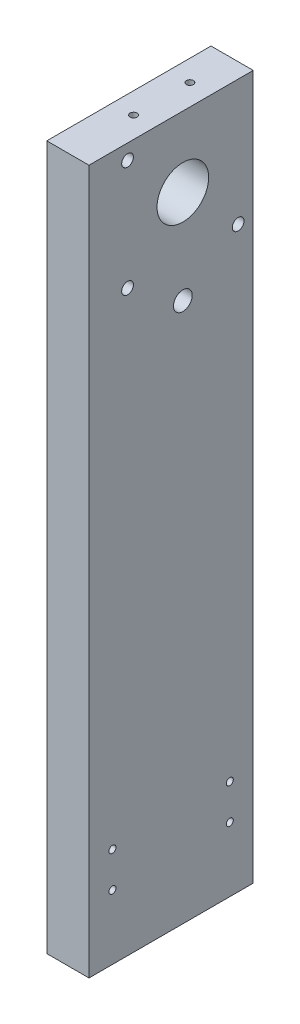
SolidWorks part; units mm, degrees
material "Bronce de aluminio"
ref_plane "Front Plane" through (0, 0, 0) normal (0, 0, 1) x (1, 0, 0)
ref_plane "Top Plane" through (0, 0, 0) normal (0, 1, 0) x (1, 0, 0)
ref_plane "Right Plane" through (0, 0, 0) normal (1, 0, 0) x (0, 0, -1)
sketch "Croquis1" plane through (0, 0, 0) normal (1, 0, 0) x (0, 0, -1)
  line L0 (35, 120) -> (5, 120) construction
  line L1 (35, -150) -> (-35, -150)
  line L2 (35, -150) -> (35, 150)
  line L3 (35, 150) -> (-35, 150)
  line L4 (-35, -150) -> (-35, 150)
  line L5 (35, -150) -> (-35, 150) construction
  line L6 (35, 150) -> (-35, -150) construction
  line L7 (5, 120) -> (5, 150) construction
  line L8 (5, 120) -> (28.57, 96.43) construction
  line L9 (5, 120) -> (-18.57, 143.57) construction
  line L10 (5, 120) -> (-18.57, 96.43) construction
  line L11 (-18.57, 143.57) -> (-18.57, 96.43) construction
  line L12 (-18.57, 96.43) -> (28.57, 96.43) construction
  line L13 (5, 120) -> (5, 80) construction
  line L14 (0, -150) -> (0, -115) construction
  line L16 (25, -122.5) -> (-25, -122.5) construction
  line L17 (25, -122.5) -> (25, -107.5) construction
  line L18 (25, -107.5) -> (-25, -107.5) construction
  line L19 (-25, -122.5) -> (-25, -107.5) construction
  line L20 (25, -122.5) -> (-25, -107.5) construction
  line L21 (25, -107.5) -> (-25, -122.5) construction
  circle A0 centre (5, 120) radius 11
  circle A1 centre (-18.57, 143.57) radius 2.5
  circle A2 centre (-18.57, 96.43) radius 2.5
  circle A3 centre (28.57, 96.43) radius 2.5
  circle A4 centre (5, 80) radius 4
  circle A5 centre (-25, -107.5) radius 1.5
  circle A6 centre (-25, -122.5) radius 1.5
  circle A7 centre (25, -122.5) radius 1.5
  circle A8 centre (25, -107.5) radius 1.5
  point P0 (0, 0)
  dimension "D4" = 22
  dimension "D6" = 5
  dimension "D8" = 8
  dimension "D12" = 3
  dimension "D1" = 300
  dimension "D2" = 70
  dimension "D3" = 30
  dimension "D5" = 47.14
  dimension "D7" = 40
  dimension "D9" = 50
  dimension "D10" = 15
  dimension "D11" = 35
sketch "Croquis2" plane through (0, 0, 0) normal (1, 0, 0) x (0, 0, -1)
  line L0 (35, 150) -> (-35, 150) construction
  line L1 (35, -150) -> (35, 150) construction
  line L2 (35, -150) -> (-35, -150) construction
  line L3 (-35, -150) -> (-35, 150) construction
  line L4 (35, 150) -> (-35, 150)
  line L5 (35, -150) -> (35, 150)
  line L6 (35, -150) -> (-35, -150)
  line L7 (-35, -150) -> (-35, 150)
  circle A0 centre (25, -122.5) radius 1.5 construction
  circle A1 centre (-25, -122.5) radius 1.5 construction
  circle A2 centre (25, -107.5) radius 1.5 construction
  circle A3 centre (-25, -107.5) radius 1.5 construction
  circle A4 centre (5, 80) radius 4 construction
  circle A5 centre (28.57, 96.43) radius 2.5 construction
  circle A6 centre (5, 120) radius 11 construction
  circle A7 centre (-18.57, 96.43) radius 2.5 construction
  circle A8 centre (-18.57, 143.57) radius 2.5 construction
  circle A9 centre (25, -122.5) radius 1.5
  circle A10 centre (-25, -122.5) radius 1.5
  circle A11 centre (25, -107.5) radius 1.5
  circle A12 centre (-25, -107.5) radius 1.5
  circle A13 centre (5, 80) radius 4
  circle A14 centre (28.57, 96.43) radius 2.5
  circle A15 centre (5, 120) radius 11
  circle A16 centre (-18.57, 96.43) radius 2.5
  circle A17 centre (-18.57, 143.57) radius 2.5
extrude "Saliente-Extruir1" add sketch "Croquis2" along normal blind 18
sketch "Croquis3" plane through (0, 150, 0) normal (0, 1, 0) x (1, 0, 0)
  line L0 (9, 35) -> (9, 5) construction
  line L2 (18, 35) -> (0, 35) construction
  line L4 (9, 5) -> (9, -7) construction
  circle A0 centre (9, -7) radius 1.5
  circle A1 centre (9, 17) radius 1.5
  dimension "D3" = 3
  dimension "D4" = 3
  dimension "D1" = 30
  dimension "D2" = 24
  dimension "D5" = 12
extrude "Cortar-Extruir1" cut sketch "Croquis3" against normal blind 14
extrude "Saliente-Extruir2" [suppressed] add sketch "Croquis1" along normal blind 9 contours A0 | L3 L4 L1 L2 | A7 | A8 | A5 | A6 | A4
sketch "Croquis4" [suppressed] plane through (0, 0, 0) normal (1, 0, 0) x (0, 0, -1)
  line L0 (35, -150) -> (-35, -150) construction
  line L1 (-35, -150) -> (-35, 150) construction
  line L2 (35, -150) -> (35, 150) construction
  line L3 (35, 150) -> (-35, 150) construction
  line L4 (35, -150) -> (-35, -150)
  line L5 (-35, -150) -> (-35, 150)
  line L6 (35, -150) -> (35, 150)
  line L7 (35, 150) -> (-35, 150)
  circle A0 centre (5, 80) radius 4 construction
  circle A1 centre (-25, -107.5) radius 1.5 construction
  circle A2 centre (-25, -122.5) radius 1.5 construction
  circle A3 centre (25, -122.5) radius 1.5 construction
  circle A4 centre (25, -107.5) radius 1.5 construction
  circle A5 centre (5, 80) radius 4
  circle A6 centre (-25, -107.5) radius 1.5
  circle A7 centre (-25, -122.5) radius 1.5
  circle A8 centre (25, -122.5) radius 1.5
  circle A9 centre (25, -107.5) radius 1.5
  circle A10 centre (5, 120) radius 4
  dimension "D1" = 8
extrude "Saliente-Extruir3" [suppressed] add sketch "Croquis4" against normal blind 9
sketch "Croquis5" [suppressed] plane through (0, 150, 0) normal (0, 1, 0) x (1, 0, 0)
  line L0 (0, 35) -> (0, 17) construction
  line L1 (9, 35) -> (-9, 35) construction
  line L2 (0, 17) -> (0, -7) construction
  circle A0 centre (0, 17) radius 1.5
  circle A1 centre (0, -7) radius 1.5
  dimension "D3" = 3
  dimension "D1" = 18
  dimension "D2" = 24
extrude "Cortar-Extruir2" [suppressed] cut sketch "Croquis5" against normal blind 14
sketch "Croquis6" [suppressed] plane through (0, 0, 0) normal (0, 0, 1) x (1, 0, 0)
  line L0 (0, 0) -> (-30, 0) construction
  line L1 (50, 125) -> (-50, 125)
  line L2 (50, 125) -> (50, -125)
  line L3 (50, -125) -> (-50, -125)
  line L4 (-50, 125) -> (-50, -125)
  line L5 (50, 125) -> (-50, -125) construction
  line L6 (50, -125) -> (-50, 125) construction
  line L7 (9, 12) -> (-9, 12) construction
  line L8 (9, 12) -> (9, -12) construction
  line L9 (9, -12) -> (-9, -12) construction
  line L10 (-9, 12) -> (-9, -12) construction
  line L11 (9, 12) -> (-9, -12) construction
  line L12 (9, -12) -> (-9, 12) construction
  line L13 (-30, 0) -> (-30, 40) construction
  line L14 (-39, 52) -> (-39, -28) construction
  line L15 (-21, 28) -> (-39, 28) construction
  line L16 (-21, 28) -> (-21, 52) construction
  line L17 (-21, 52) -> (-39, 52) construction
  line L18 (-39, 28) -> (-39, 52) construction
  line L19 (-21, 28) -> (-39, 52) construction
  line L20 (-21, 52) -> (-39, 28) construction
  circle A0 centre (-9, 12) radius 1.5
  circle A1 centre (9, 12) radius 1.5
  circle A2 centre (9, -12) radius 1.5
  circle A3 centre (-9, -12) radius 1.5
  circle A4 centre (-21, 28) radius 1.5
  circle A5 centre (-39, 28) radius 1.5
  circle A6 centre (-21, 52) radius 1.5
  circle A7 centre (-39, 52) radius 1.5
  circle A8 centre (21, 52) radius 1.5
  circle A9 centre (39, 52) radius 1.5
  circle A10 centre (21, 28) radius 1.5
  circle A11 centre (39, 28) radius 1.5
  circle A12 centre (-39, -28) radius 1.5
  circle A13 centre (-21, -28) radius 1.5
  circle A14 centre (-39, -52) radius 1.5
  circle A15 centre (-21, -52) radius 1.5
  circle A16 centre (21, -28) radius 1.5
  circle A17 centre (21, -52) radius 1.5
  circle A18 centre (39, -28) radius 1.5
  circle A19 centre (39, -52) radius 1.5
  point P0 (0, 0)
  point P6 (0, 0)
  dimension "D7" = 3
  dimension "D9" = 60
  dimension "D1" = 100
  dimension "D2" = 255
  dimension "D3" = 18
  dimension "D4" = 24
  dimension "D5" = 30
  dimension "D6" = 40
  dimension "D11" = 80
  dimension "D8" = 2
  dimension "D10" = 2
extrude "Saliente-Extruir4" [suppressed] add sketch "Croquis6" along normal blind 16
sketch "Croquis7" [suppressed] plane through (0, 0, 0) normal (0, 0, 1) x (1, 0, 0)
  line L0 (50, 125) -> (-50, 125) construction
  line L1 (50, -125) -> (50, 125) construction
  line L2 (-50, -125) -> (50, -125) construction
  line L3 (-50, 125) -> (-50, -125) construction
  line L4 (50, 125) -> (-50, 125)
  line L5 (50, -125) -> (50, 125)
  line L6 (-50, -125) -> (50, -125)
  line L7 (-50, 125) -> (-50, -125)
extrude "Saliente-Extruir5" [suppressed] add sketch "Croquis7" along normal blind 2
sketch "Croquis8" [suppressed] plane through (0, 0, 0) normal (1, 0, 0) x (0, 0, -1)
  line L0 (15, 0) -> (-15, 0)
  line L1 (-15, 0) -> (-15, 6)
  line L2 (-15, 6) -> (-7, 6)
  line L3 (-7, 6) -> (-7, 25)
  line L4 (-7, 25) -> (-1, 25)
  line L5 (-1, 25) -> (-1, 13)
  line L6 (-1, 13) -> (1, 13)
  line L7 (1, 13) -> (1, 25)
  line L8 (1, 25) -> (7, 25)
  line L9 (7, 25) -> (7, 6)
  line L10 (7, 6) -> (15, 6)
  line L11 (15, 6) -> (15, 0)
  line L12 (0, 0) -> (0, 10) construction
  circle A0 centre (0, 10) radius 4
  point P4 (0, 0)
  dimension "D7" = 8
  dimension "D1" = 30
  dimension "D2" = 25
  dimension "D3" = 8
  dimension "D4" = 2
  dimension "D5" = 12
  dimension "D6" = 10
  dimension "D8" = 6
extrude "Saliente-Extruir6" [suppressed] add sketch "Croquis8" along normal mid plane 16 contours L12 L0 L11 L10 L9 L8 L7 A0 | L0 L12 A0 L5 L4 L3 L2 L1
sketch "Croquis9" [suppressed] plane through (0, 6, 0) normal (0, 1, 0) x (1, 0, 0)
  line L0 (0, -12) -> (0, 12) construction
  circle A0 centre (0, 12) radius 1.5
  circle A1 centre (0, -12) radius 1.5
  point P4 (0, 0)
  dimension "D2" = 3
  dimension "D1" = 24
extrude "Cortar-Extruir3" [suppressed] cut sketch "Croquis9" against normal up to next
sketch "Croquis10" [suppressed] plane through (0, 125, 0) normal (0, 1, 0) x (1, 0, 0)
  line L0 (0, 0) -> (0, -8) construction
  line L1 (16.5, -8) -> (-16.5, -8) construction
  line L2 (-16.5, -8) -> (-33, -8) construction
  line L3 (16.5, -8) -> (33, -8) construction
  circle A0 centre (-33, -8) radius 1.5
  circle A1 centre (-16.5, -8) radius 1.5
  circle A2 centre (0, -8) radius 1.5
  circle A3 centre (16.5, -8) radius 1.5
  circle A4 centre (33, -8) radius 1.5
  point P6 (0, -8)
  dimension "D4" = 3
  dimension "D1" = 8
  dimension "D2" = 33
  dimension "D3" = 16.5
sketch "Croquis11" [suppressed] plane through (0, 125, 0) normal (0, 1, 0) x (1, 0, 0)
  circle A0 centre (33, -8) radius 1.5 construction
  circle A1 centre (16.5, -8) radius 1.5 construction
  circle A2 centre (0, -8) radius 1.5 construction
  circle A3 centre (-16.5, -8) radius 1.5 construction
  circle A4 centre (33, -8) radius 1.5
  circle A5 centre (16.5, -8) radius 1.5
  circle A6 centre (0, -8) radius 1.5
  circle A7 centre (-16.5, -8) radius 1.5
  circle A8 centre (-33, -8) radius 1.5 construction
  circle A9 centre (-33, -8) radius 1.5
  point P0 (-33, -8)
extrude "Cortar-Extruir4" [suppressed] cut sketch "Croquis11" against normal blind 15
sketch "Croquis12" [suppressed] plane through (0, -125, 0) normal (0, -1, 0) x (1, 0, 0)
  circle A0 centre (-33, 8) radius 1.5 construction
  circle A1 centre (-16.5, 8) radius 1.5 construction
  circle A2 centre (0, 8) radius 1.5 construction
  circle A3 centre (16.5, 8) radius 1.5 construction
  circle A4 centre (33, 8) radius 1.5 construction
  circle A5 centre (-33, 8) radius 1.5
  circle A6 centre (-16.5, 8) radius 1.5
  circle A7 centre (0, 8) radius 1.5
  circle A8 centre (16.5, 8) radius 1.5
  circle A9 centre (33, 8) radius 1.5
extrude "Cortar-Extruir5" [suppressed] cut sketch "Croquis12" against normal blind 15
equation "\"D1@Croquis5\"=30-12"
